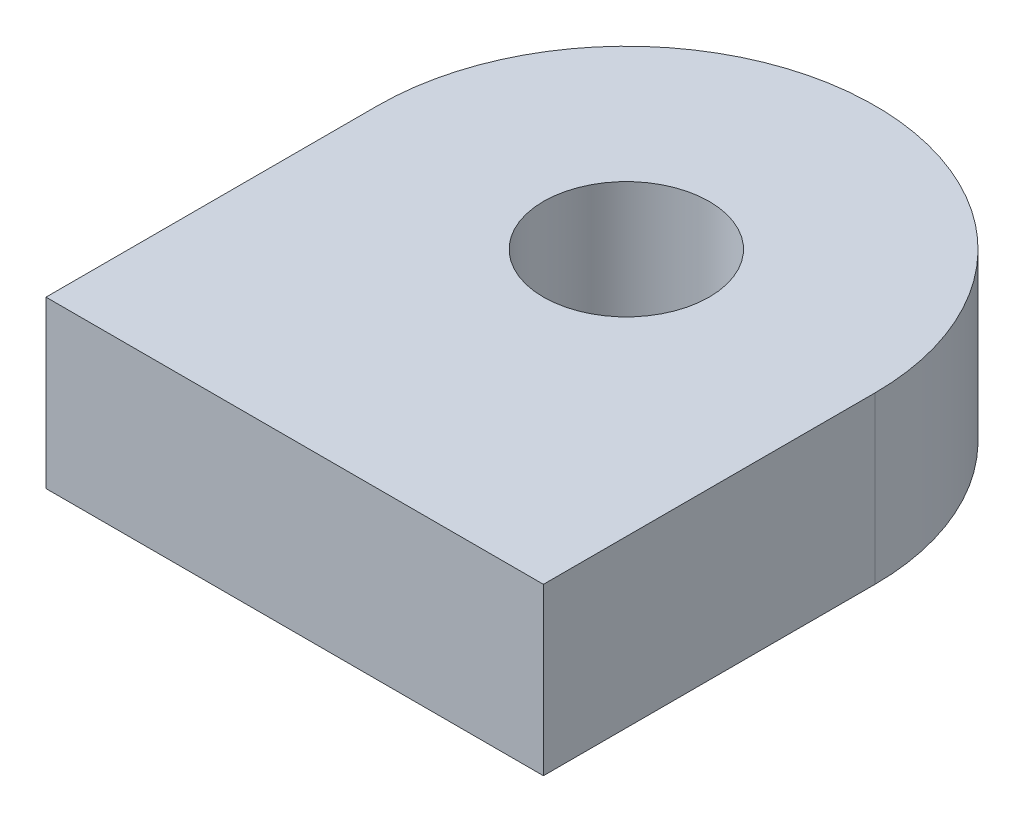
SolidWorks part; units mm, degrees
material "Plain Carbon Steel"
ref_plane "Front Plane" through (0, 0, 0) normal (0, 0, 1) x (1, 0, 0)
ref_plane "Top Plane" through (0, 0, 0) normal (0, 1, 0) x (1, 0, 0)
ref_plane "Right Plane" through (0, 0, 0) normal (1, 0, 0) x (0, 0, -1)
sketch "Sketch1" plane through (0, 0, 0) normal (0, 1, 0) x (1, 0, 0)
  line L0 (-19.05, 0) -> (-6.35, 0) construction
  line L1 (-19.05, 0) -> (-19.05, -25.4)
  line L2 (-19.05, -25.4) -> (19.05, -25.4)
  line L3 (19.05, -25.4) -> (19.05, 0)
  line L4 (6.35, 0) -> (19.05, 0) construction
  arc A0 (19.05, 0) -> (-19.05, 0) centre (0, 0) ccw
  circle A1 centre (0, 0) radius 6.35
  dimension "D2" = 12.7
  dimension "D1" = 38.1
  dimension "D3" = 25.4
extrude "Fastener" add sketch "Sketch1" along normal blind 12.7
